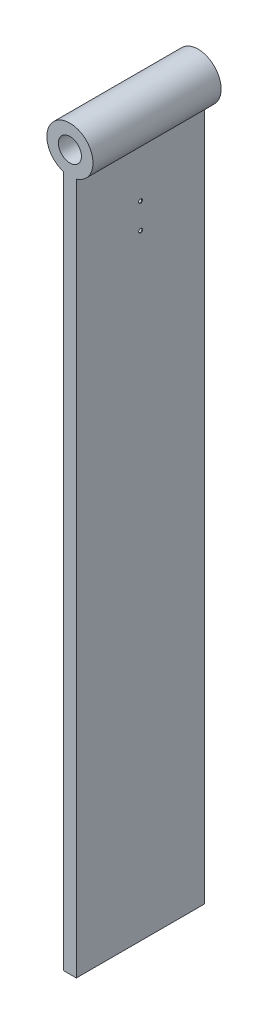
SolidWorks part; units mm, degrees
ref_plane "前视基准面" through (0, 0, 0) normal (0, 0, 1) x (1, 0, 0)
ref_plane "上视基准面" through (0, 0, 0) normal (0, 1, 0) x (1, 0, 0)
ref_plane "右视基准面" through (0, 0, 0) normal (1, 0, 0) x (0, 0, -1)
sketch "草图1" plane through (0, 0, 0) normal (0, 0, 1) x (1, 0, 0)
  line L0 (0, 0) -> (5, 0)
  line L1 (5, 0) -> (5, 540)
  line L2 (0, 0) -> (-5, 0)
  line L3 (-5, 0) -> (-5, 540)
  arc A0 (5, 540) -> (-5, 540) centre (0, 557.2916) ccw
  point P6 (0, 0)
  point P8 (0, 0)
  point P9 (0, 0)
  point P10 (0, 0)
  dimension "D3" = 18
  dimension "D4" = 5
  dimension "D1" = 5
  dimension "D2" = 540
  dimension "D5" = 540
extrude "凸台-拉伸1" add sketch "草图1" along normal blind 100
sketch "草图2" plane through (0, 0, 100) normal (0, 0, 1) x (1, 0, 0)
  circle A0 centre (0, 557.2916) radius 9
extrude "切除-拉伸1" cut sketch "草图2" against normal blind 100
hole_wizard "M3 螺纹孔3" positions "3D草图1" profile "草图7" tap size "M3" standard "GB" end condition through all
sketch3d "3D草图1"
  point P0 (5, 500, 49.9389)
  point P3 (0, 0, 0)
sketch "草图7" plane through (5, 500, 49.9389) normal (0, 1, 0) x (0, 0, -1)
  line L0 (0, 0) -> (0, 23)
  line L1 (0, 23) -> (1.25, 23)
  line L2 (1.25, 23) -> (1.25, 0.275)
  line L3 (1.25, 0.275) -> (1.525, 0)
  line L5 (1.525, 0) -> (0, 0)
  line L6 (-1.25, 0.275) -> (-1.525, 0) construction
  line L11 (0, -6.35) -> (0, 107.95) construction
  dimension "通孔螺纹孔钻头直径" = 2.5
  dimension "通孔螺纹孔钻头深度" = 23
  dimension "近端锥形沉头孔直径" = 3.05
  dimension "近端锥形沉头孔角度" = 90
cosmetic thread "孔螺蚊线5" parameters "D2"=3
hole_wizard "M3 螺纹孔4" positions "3D草图2" profile "草图8" tap size "M3" standard "GB" end condition through all
sketch3d "3D草图2"
  point P0 (5, 480, 49.8903)
  point P2 (5, 480, 49.8903)
  point P4 (5, 480, 49.8903)
sketch "草图8" plane through (5, 480, 49.8903) normal (0, 1, 0) x (0, 0, -1)
  line L0 (0, 0) -> (0, 23)
  line L1 (0, 23) -> (1.25, 23)
  line L2 (1.25, 23) -> (1.25, 0.275)
  line L3 (1.25, 0.275) -> (1.525, 0)
  line L5 (1.525, 0) -> (0, 0)
  line L6 (-1.25, 0.275) -> (-1.525, 0) construction
  line L11 (0, -6.35) -> (0, 107.95) construction
  dimension "通孔螺纹孔钻头直径" = 2.5
  dimension "通孔螺纹孔钻头深度" = 23
  dimension "近端锥形沉头孔直径" = 3.05
  dimension "近端锥形沉头孔角度" = 90
cosmetic thread "孔螺蚊线6" parameters "D2"=3
cosmetic thread "孔螺蚊线7" parameters "D2"=3
cosmetic thread "孔螺蚊线8" parameters "D2"=3
